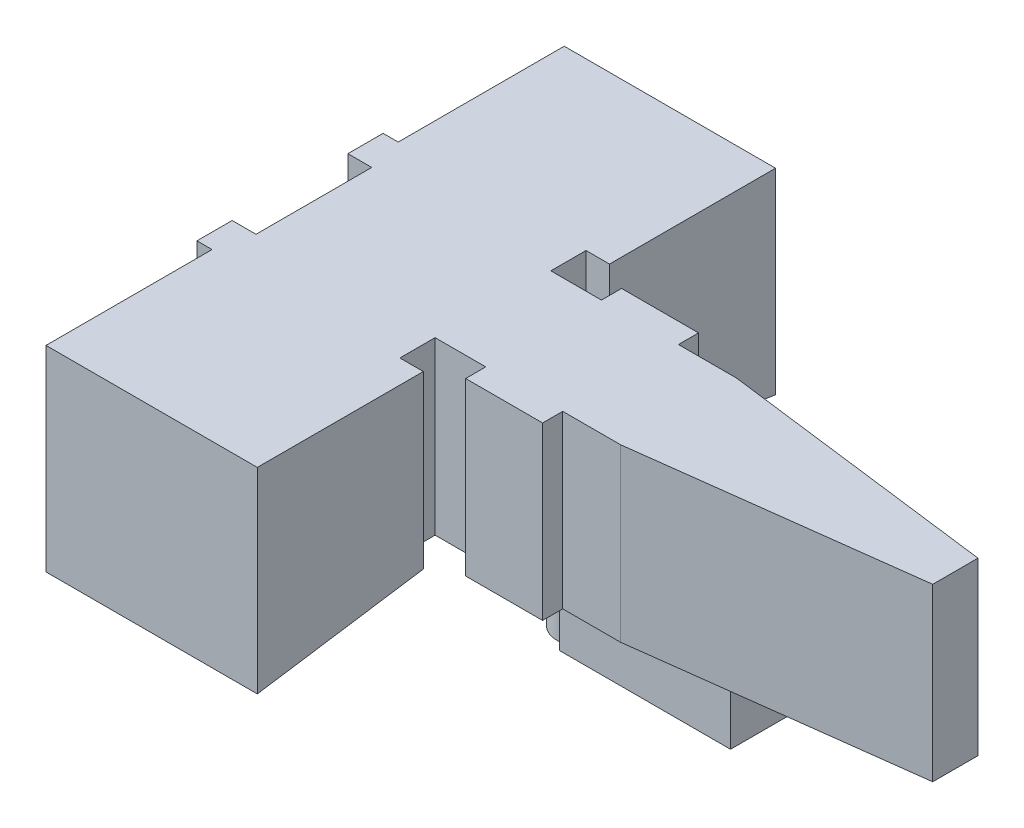
SolidWorks part; units mm, degrees
ref_plane "Front Plane" through (0, 0, 0) normal (0, 0, 1) x (1, 0, 0)
ref_plane "Top Plane" through (0, 0, 0) normal (0, 1, 0) x (1, 0, 0)
ref_plane "Right Plane" through (0, 0, 0) normal (1, 0, 0) x (0, 0, -1)
sketch "Sketch1" plane through (0, 0, 0) normal (0, 1, 0) x (1, 0, 0)
  line L0 (237.3919, 410.6407) -> (1037.0042, 340.6837) construction
  line L1 (38.8879, 32.6465) -> (33.8554, 32.6465)
  line L2 (52.2879, 21.1465) -> (79.8081, 24.6465)
  line L3 (46.5379, 21.1465) -> (52.2879, 21.1465)
  line L5 (33.8554, 21.1465) -> (38.8879, 21.1465)
  line L9 (52.2879, 32.6465) -> (46.5379, 32.6465)
  line L14 (79.8081, 29.1465) -> (79.8081, 24.6465)
  line L18 (16.0581, 21.1465) -> (16.0581, 32.6465)
  line L20 (46.5379, 32.6465) -> (46.5379, 34.6465)
  line L21 (46.5379, 34.6465) -> (38.8879, 34.6465)
  line L22 (38.8879, 32.6465) -> (38.8879, 34.6465)
  line L24 (38.8879, 21.1465) -> (38.8879, 19.1465)
  line L25 (38.8879, 19.1465) -> (46.5379, 19.1465)
  line L26 (46.5379, 21.1465) -> (46.5379, 19.1465)
  line L27 (52.2879, 32.6465) -> (79.8081, 29.1465)
  line L30 (33.8554, 21.1465) -> (33.8554, 17.6465)
  line L32 (13.6871, 21.1465) -> (13.6871, 17.6465)
  line L34 (33.8554, 32.6465) -> (33.8554, 36.1465)
  line L36 (13.6871, 32.6465) -> (13.6871, 36.1465)
  line L37 (15.1871, 1.1465) -> (36.1871, 1.1465)
  line L38 (15.1871, 1.1465) -> (15.1871, 17.6465)
  line L39 (33.8554, 17.6465) -> (36.1871, 17.6465)
  line L40 (36.1871, 1.1465) -> (36.1871, 17.6465)
  line L41 (33.8554, 36.1465) -> (36.1871, 36.1465)
  line L42 (15.1871, 36.1465) -> (15.1871, 52.6465)
  line L43 (15.1871, 52.6465) -> (36.1871, 52.6465)
  line L44 (36.1871, 36.1465) -> (36.1871, 52.6465)
  line L46 (15.1871, 36.1465) -> (13.6871, 36.1465)
  line L47 (16.0581, 32.6465) -> (13.6871, 32.6465)
  line L48 (16.0581, 21.1465) -> (13.6871, 21.1465)
  line L49 (15.1871, 17.6465) -> (13.6871, 17.6465)
  dimension "D2" = 11.5
  dimension "D4" = 2
  dimension "D5" = 2
  dimension "D9" = 7.65
  dimension "D10" = 7.65
  dimension "D13" = 3.5
  dimension "D14" = 3.5
  dimension "D15" = 1.5
  dimension "D16" = 20
  dimension "D17" = 20
  dimension "D18" = 21
  dimension "D19" = 21
extrude "Boss-Extrude1" add sketch "Sketch1" along normal blind 17
sketch "Sketch2" plane through (0, 0, 0) normal (0, -1, 0) x (1, 0, 0)
  line L0 (42.7129, -19.1465) -> (42.7129, -34.6465) construction
  line L1 (38.8879, -19.1465) -> (46.5379, -19.1465) construction
  line L2 (46.5379, -34.6465) -> (38.8879, -34.6465) construction
  line L3 (43.7129, -29.1878) -> (43.7129, -30.1465)
  line L6 (45.2129, -30.1465) -> (60.7129, -30.1465)
  line L7 (60.7129, -26.8965) -> (60.7129, -30.1465)
  line L9 (60.7129, -26.8965) -> (60.7129, -23.6465)
  line L10 (60.7129, -23.6465) -> (45.2129, -23.6465)
  line L12 (45.2129, -23.6465) -> (43.7129, -23.6465)
  line L14 (45.2129, -30.1465) -> (43.7129, -30.1465)
  line L15 (43.7129, -23.6465) -> (43.7129, -24.6052)
  arc A0 (43.7129, -24.6052) -> (43.7129, -29.1878) centre (42.7129, -26.8965) ccw
  dimension "D1" = 15.5
  dimension "D2" = 3.25
  dimension "D3" = 3.25
  dimension "D4" = 1.5
extrude "Boss-Extrude2" add sketch "Sketch2" along normal blind 6.25
sketch "Sketch3" plane through (15.1871, 0, 0) normal (-1, 0, 0) x (0, 0, 1)
  line L0 (-1.1465, 0) -> (-1.1465, -2.5)
  line L1 (-1.1465, -2.5) -> (-17.6465, 0)
  line L2 (-1.1465, 0) -> (-17.6465, 0)
  line L3 (-36.1465, 0) -> (-52.6465, 0)
  line L4 (-52.6465, 0) -> (-52.6465, -2.5)
  line L5 (-52.6465, -2.5) -> (-36.1465, 0)
  dimension "D1" = 2.5
  dimension "D2" = 2.5
extrude "Boss-Extrude3" add sketch "Sketch3" against normal blind 21
